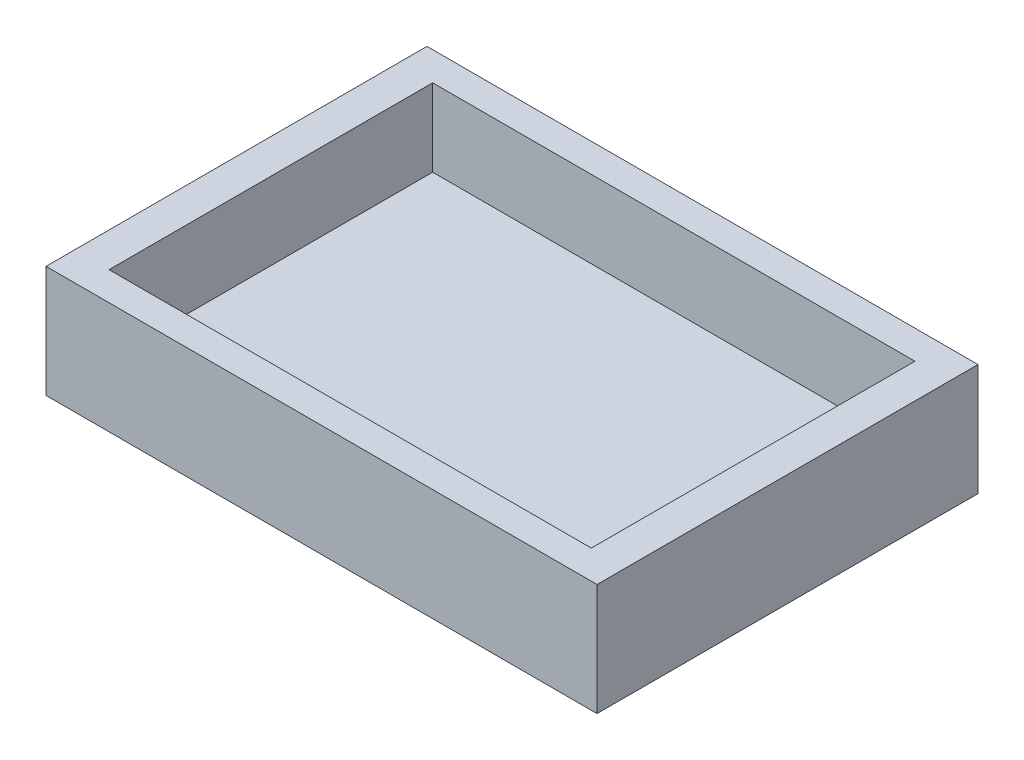
SolidWorks part; units mm, degrees
material "ABS"
ref_plane "Front Plane" through (0, 0, 0) normal (0, 0, 1) x (1, 0, 0)
ref_plane "Top Plane" through (0, 0, 0) normal (0, 1, 0) x (1, 0, 0)
ref_plane "Right Plane" through (0, 0, 0) normal (1, 0, 0) x (0, 0, -1)
sketch "Sketch1" plane through (0, 0, 0) normal (0, 1, 0) x (1, 0, 0)
  line L1 (48.8, 33.2187) -> (-48.8, 33.2187)
  line L2 (48.8, 33.2187) -> (48.8, -33.2187)
  line L3 (48.8, -33.2187) -> (-48.8, -33.2187)
  line L4 (-48.8, 33.2187) -> (-48.8, -33.2187)
  line L5 (48.8, 33.2187) -> (-48.8, -33.2187) construction
  line L6 (48.8, -33.2187) -> (-48.8, 33.2187) construction
  point P0 (0, 0)
  dimension "D1" = 97.6
  dimension "D2" = 66.4375
extrude "Boss-Extrude1" add sketch "Sketch1" along normal blind 6
sketch "Sketch3" plane through (0, 6, 0) normal (0, 1, 0) x (1, 0, 0)
  line L0 (48.8, -33.2187) -> (48.8, 33.2187) construction
  line L1 (30.8, 27) -> (-24.2, 27)
  line L2 (30.8, 27) -> (30.8, -27)
  line L3 (30.8, -27) -> (-24.2, -27)
  line L4 (-24.2, 27) -> (-24.2, -27)
  line L5 (30.8, 27) -> (-24.2, -27) construction
  line L6 (30.8, -27) -> (-24.2, 27) construction
  point P0 (3.3, 0)
  dimension "D1" = 54
  dimension "D2" = 55
  dimension "D3" = 0
  dimension "D4" = 18
sketch "Sketch4" plane through (0, 6, 0) normal (0, 1, 0) x (1, 0, 0)
  line L0 (30.8, -27) -> (30.8, -33.2187)
  line L1 (-48.8, -33.2187) -> (48.8, -33.2187) construction
  line L2 (30.8, -33.2187) -> (30.8, 33.2187)
  line L3 (48.8, 33.2187) -> (-48.8, 33.2187) construction
  line L4 (30.8, 33.2187) -> (30.8, 27)
  line L5 (30.8, 27) -> (48.8, 27)
  line L6 (48.8, -33.2187) -> (48.8, 33.2187) construction
  line L7 (48.8, 27) -> (-48.8, 27)
  line L8 (-48.8, 33.2187) -> (-48.8, -33.2187) construction
  line L9 (-48.8, 27) -> (-24.2, 27)
  line L10 (-24.2, 27) -> (-24.2, 33.2187)
  line L11 (-24.2, 33.2187) -> (-24.2, -33.2187)
  line L13 (-24.2, -33.2187) -> (-48.8, -33.2187)
  line L14 (-24.2, -33.2187) -> (-24.2, 33.2187)
  line L15 (-24.2, 33.2187) -> (-48.8, 33.2187)
  line L16 (-48.8, -33.2187) -> (-48.8, 33.2187)
  line L17 (-48.8, 33.2187) -> (48.8, 33.2187)
  line L18 (-48.8, 33.2187) -> (-48.8, 27)
  line L19 (-48.8, 27) -> (48.8, 27)
  line L20 (48.8, 33.2187) -> (48.8, 27)
  line L21 (48.8, 33.2187) -> (30.8, 33.2187)
  line L22 (48.8, 33.2187) -> (48.8, -33.2187)
  line L23 (48.8, -33.2187) -> (30.8, -33.2187)
  line L24 (30.8, 33.2187) -> (30.8, -33.2187)
  line L25 (48.8, -33.2187) -> (-48.8, -33.2187)
  line L26 (48.8, -33.2187) -> (48.8, -27)
  line L27 (48.8, -27) -> (-48.8, -27)
  line L28 (-48.8, -33.2187) -> (-48.8, -27)
  line M1 (-48.8, 33.2187) -> (-48.8, -33.2187)
  line M2 (-48.8, -33.2187) -> (48.8, -33.2187)
  line M3 (48.8, -33.2187) -> (48.8, 33.2187)
  line M4 (48.8, 33.2187) -> (-48.8, 33.2187)
extrude "Boss-Extrude2" add sketch "Sketch4" along normal blind 13.5 contours L27 L11 L7 M1 | L14 L27 L16 M2 | L0 L27 L14 M2 | L27 L0 M3 M2 | L27 L22 L5 L2 | L2 L5 M3 M4 | L7 L10 M4 M1 | L10 L7 L2 M4
sketch "Sketch5" plane through (0, 19.5, 0) normal (0, 1, 0) x (1, 0, 0)
  line L0 (-46.8936, -20) -> (-12.1997, -20)
  line L1 (-46.8936, -20) -> (-46.8936, 10)
  line L2 (-12.1997, -20) -> (-12.1997, 10)
  line L3 (-46.8936, 10) -> (-12.1997, 10)
  line L4 (-46.8936, -20) -> (-12.1997, 10) construction
  line L5 (-12.1997, -20) -> (-46.8936, 10) construction
  point P1 (-29.5467, -5)
  dimension "D1" = 30
  dimension "D2" = 5
extrude "Cut-Extrude1" [suppressed] cut sketch "Sketch5" against normal blind 13.5
sketch "Sketch6" plane through (0, 19.5, 0) normal (0, 1, 0) x (1, 0, 0)
  line L0 (48.8, -33.2187) -> (48.8, 33.2187) construction
  line L1 (48.8, 28.2187) -> (-48.8, 28.2187)
  line L2 (48.8, 28.2187) -> (48.8, -28.2187)
  line L3 (48.8, -28.2187) -> (-48.8, -28.2187)
  line L4 (-48.8, 28.2187) -> (-48.8, -28.2187)
  line L5 (-48.8, 33.2187) -> (-48.8, -33.2187) construction
  line L6 (48.8, 33.2187) -> (-48.8, 33.2187) construction
  line L7 (-48.8, -33.2187) -> (48.8, -33.2187) construction
  dimension "D1" = 5
  dimension "D2" = 5
extrude "Cut-Extrude2" cut sketch "Sketch6" against normal blind 13.5
sketch "Sketch7" plane through (48.8, 0, 0) normal (1, 0, 0) x (0, 0, -1)
  line L1 (33.2187, 0) -> (-33.2187, 0)
  line L2 (33.2187, 0) -> (33.2187, 19.5)
  line L3 (33.2187, 19.5) -> (-33.2187, 19.5)
  line L4 (-33.2187, 0) -> (-33.2187, 19.5)
extrude "Cut-Extrude3" cut sketch "Sketch7" against normal blind 0.75
sketch "Sketch8" plane through (-48.8, 0, 0) normal (-1, 0, 0) x (0, 0, 1)
  line L1 (-33.2187, 0) -> (33.2187, 0)
  line L2 (-33.2187, 0) -> (-33.2187, 19.5)
  line L3 (-33.2187, 19.5) -> (33.2187, 19.5)
  line L4 (33.2187, 0) -> (33.2187, 19.5)
extrude "Cut-Extrude4" cut sketch "Sketch8" against normal blind 0.75
sketch "Sketch9" plane through (0, 6, 0) normal (0, 1, 0) x (1, 0, 0)
  line L0 (-48.05, -28.2187) -> (48.05, -28.2187) construction
  line L1 (-48.05, 28.2187) -> (-42.05, 28.2187)
  line L2 (-48.05, 28.2187) -> (-48.05, -28.2187)
  line L3 (-48.05, -28.2187) -> (-42.05, -28.2187)
  line L4 (-42.05, 28.2187) -> (-42.05, -28.2187)
  line L5 (0, 28.2187) -> (0, -28.2187) construction
  line L6 (48.05, 28.2187) -> (-48.05, 28.2187) construction
  line L7 (48.05, -28.2187) -> (42.05, -28.2187)
  line L8 (48.05, 28.2187) -> (48.05, -28.2187)
  line L9 (48.05, 28.2187) -> (42.05, 28.2187)
  line L10 (42.05, 28.2187) -> (42.05, -28.2187)
  dimension "D1" = 6
extrude "Boss-Extrude3" add sketch "Sketch9" along normal blind 13.5
